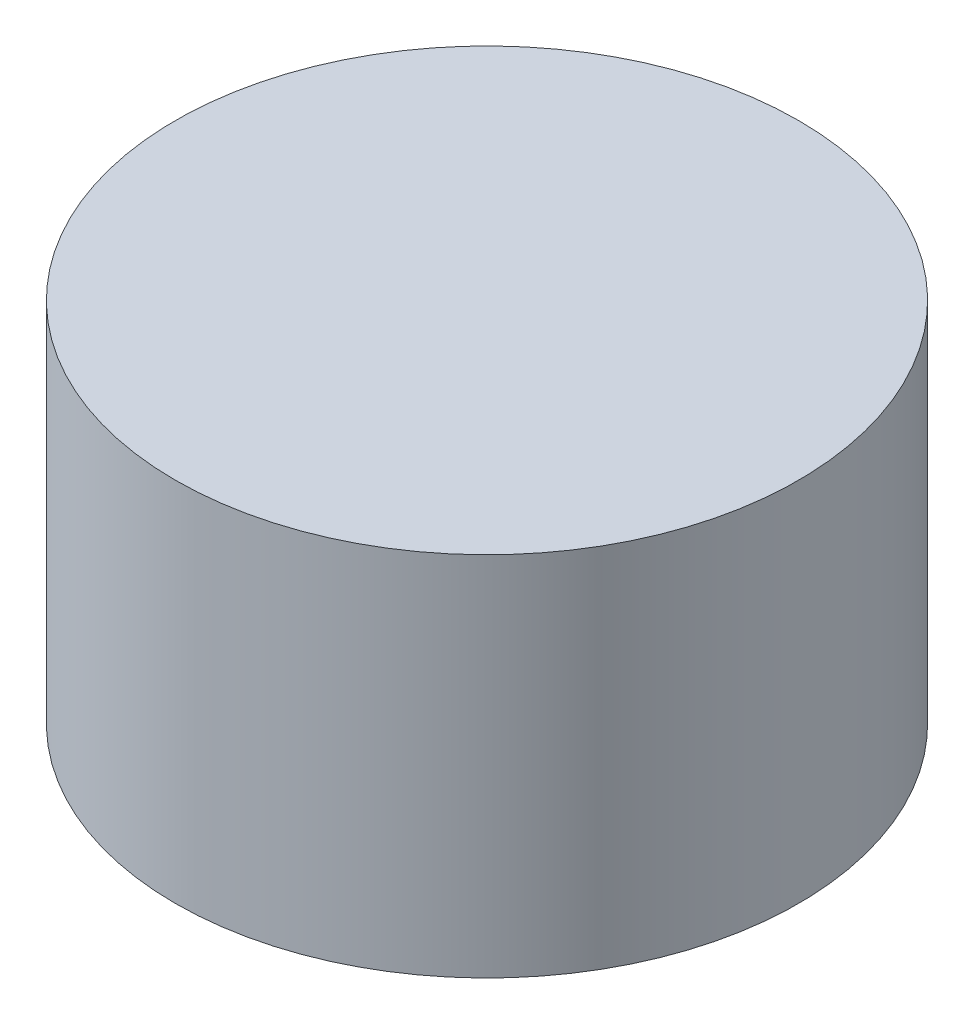
SolidWorks part; units mm, degrees
ref_plane "Front Plane" through (0, 0, 0) normal (0, 0, 1) x (1, 0, 0)
ref_plane "Top Plane" through (0, 0, 0) normal (0, 1, 0) x (1, 0, 0)
ref_plane "Right Plane" through (0, 0, 0) normal (1, 0, 0) x (0, 0, -1)
sketch "Sketch2" plane through (0, 0, 0) normal (0, 1, 0) x (1, 0, 0)
  circle A0 centre (0, 0) radius 10.795
  dimension "D1" = 21.59
extrude "Boss-Extrude1" add sketch "Sketch2" along normal blind 12.7
